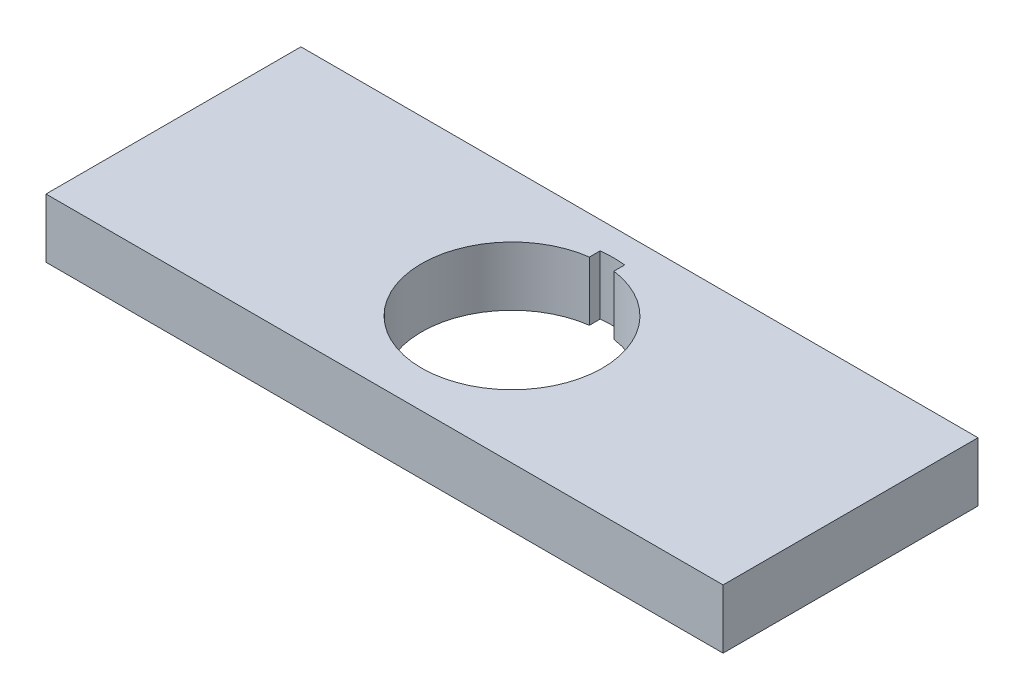
SolidWorks part; units mm, degrees
ref_plane "Front Plane" through (0, 0, 0) normal (0, 0, 1) x (1, 0, 0)
ref_plane "Top Plane" through (0, 0, 0) normal (0, 1, 0) x (1, 0, 0)
ref_plane "Right Plane" through (0, 0, 0) normal (1, 0, 0) x (0, 0, -1)
sketch "Sketch1" plane through (0, 0, 0) normal (0, 0, 1) x (1, 0, 0)
  line L0 (-33.2, -62.5) -> (-33.2, 62.5) construction
  line L1 (33.2, 62.5) -> (-33.2, 62.5)
  line L2 (33.2, 62.5) -> (33.2, 56.7)
  line L3 (33.2, 56.7) -> (-33.2, 56.7)
  line L4 (-33.2, 62.5) -> (-33.2, 56.7)
  dimension "D1" = 5.8
extrude "Boss-Extrude1" add sketch "Sketch1" along normal up to surface (25 mm away)
sketch "Sketch2" plane through (0, 62.5, 0) normal (0, 1, 0) x (1, 0, 0)
  line L0 (-33.2, 0) -> (33.2, -25) construction
  circle A0 centre (0, -12.5) radius 8.875
  dimension "D1" = 17.75
extrude "Cut-Extrude1" cut sketch "Sketch2" against normal through all
sketch "Sketch3" plane through (0, 56.7, 0) normal (0, -1, 0) x (1, 0, 0)
  line L6 (-1.2, 3.7065) -> (1.2, 3.7065)
  line L7 (1.2, 2.6579) -> (1.2, 3.7065)
  line L8 (-1.2, 2.6579) -> (-1.2, 3.7065)
  circle A1 centre (0, 12.5) radius 8.875 construction
  circle A2 centre (0, 12.5) radius 9.915
  arc A3 (-1.2, 2.6579) -> (1.2, 2.6579) centre (0, 12.5) ccw
  point P15 (0, 3.7065)
  dimension "D2" = 2.4
  dimension "D1" = 1.04
extrude "Cut-Extrude2" cut sketch "Sketch3" against normal through all
